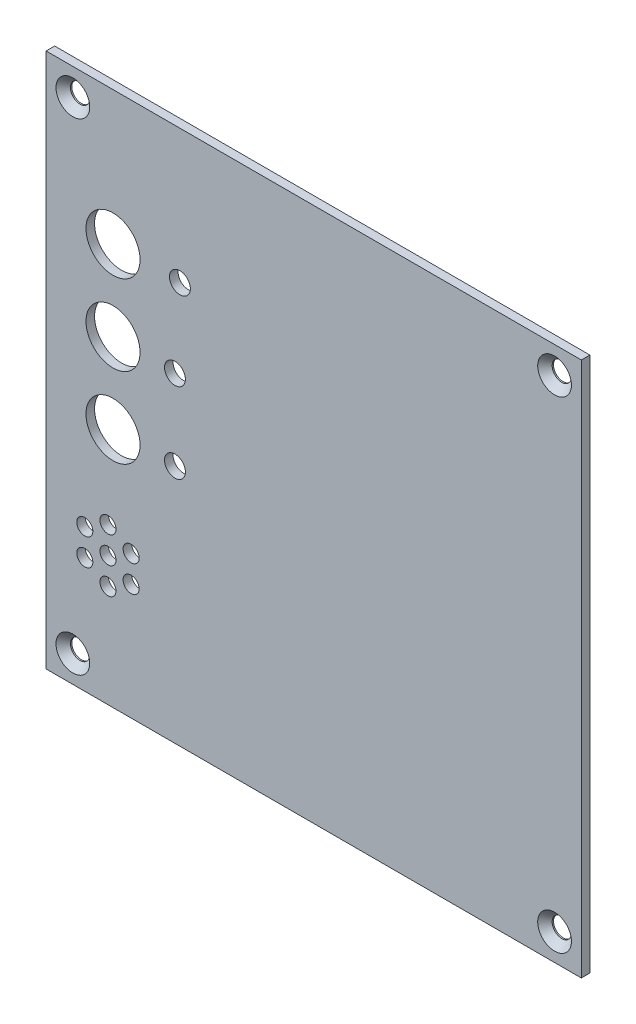
SolidWorks part; units mm, degrees
material "Perspex (TM) Plaque acrylique coulée"
ref_plane "Plan de face" through (0, 0, 0) normal (0, 0, 1) x (1, 0, 0)
ref_plane "Plan de dessus" through (0, 0, 0) normal (0, 1, 0) x (1, 0, 0)
ref_plane "Plan de droite" through (0, 0, 0) normal (1, 0, 0) x (0, 0, -1)
sketch "Esquisse1" plane through (0, 0, 0) normal (0, 0, 1) x (1, 0, 0)
  line L1 (0, 0) -> (100, 0)
  line L2 (0, 0) -> (0, 100)
  line L3 (0, 100) -> (100, 100)
  line L4 (100, 0) -> (100, 100)
  dimension "D1" = 100
  dimension "D2" = 100
extrude "Boss.-Extru.1" add sketch "Esquisse1" along normal blind 1.6
hole_wizard "Fraisage pour vis à tête fraisée M31" positions "Esquisse3D1" profile "Esquisse3" countersink size "M3" standard "ISO" end condition through all
sketch3d "Esquisse3D1"
  line L0 (100, 100, 1.6) -> (0, 100, 1.6) construction
  line L1 (0, 100, 1.6) -> (0, 0, 1.6) construction
  line L2 (100, 0, 1.6) -> (100, 100, 1.6) construction
  line L3 (0, 0, 1.6) -> (100, 0, 1.6) construction
  point P0 (5, 95, 1.6)
  point P2 (95, 95, 1.6)
  point P4 (95, 5, 1.6)
  point P6 (5, 5, 1.6)
  dimension "D1" = 5
  dimension "D2" = 5
  dimension "D3" = 5
  dimension "D4" = 5
  dimension "D5" = 5
  dimension "D6" = 5
  dimension "D7" = 5
  dimension "D8" = 5
sketch "Esquisse3" plane through (5, 95, 1.6) normal (1, 0, 0) x (0, -1, 0)
  line L0 (0, 0) -> (0, 1.6)
  line L1 (0, 1.6) -> (1.8, 1.6)
  line L2 (1.8, 1.6) -> (1.8, 1.35)
  line L3 (1.8, 1.35) -> (3.15, 0)
  line L5 (3.15, 0) -> (0, 0)
  line L6 (-1.8, 1.35) -> (-3.15, 0) construction
  line L11 (0, -6.35) -> (0, 107.95) construction
  dimension "Diamètre du perçage jusqu'au prochain" = 3.6
  dimension "Profondeur du perçage jusqu'au prochain" = 1.6
  dimension "Diamètre du fraisage entrant" = 6.3
  dimension "Angle du fraisage entrant" = 90
sketch "Esquisse4" plane through (0, 0, 1.6) normal (0, 0, 1) x (1, 0, 0)
  line L0 (0, 0) -> (100, 0) construction
  line L2 (0, 100) -> (0, 0) construction
  circle A1 centre (11.557, 24.13) radius 1.5
  circle A3 centre (11.557, 29.13) radius 1.5
  circle A4 centre (15.8871, 26.63) radius 1.5
  circle A5 centre (15.8871, 21.63) radius 1.5
  circle A6 centre (11.557, 19.13) radius 1.5
  circle A7 centre (7.2269, 21.63) radius 1.5
  circle A8 centre (7.2269, 26.63) radius 1.5
  circle A12 centre (12.5, 75) radius 5.05
  circle A13 centre (12.5, 60) radius 5.05
  circle A14 centre (12.5, 45) radius 5.05
  circle A15 centre (25, 75) radius 1.95
  circle A16 centre (24.0718, 59.8692) radius 1.95
  circle A17 centre (24.0718, 44.8692) radius 1.95
  point P25 (11.557, 24.13)
  point P31 (0, 0)
  point P32 (0, 0)
  point P34 (36.5794, 27.5686)
  dimension "D1" = 25
  dimension "D3" = 11.557
  dimension "D5" = 6
  dimension "D7" = 3
  dimension "D2" = 75
  dimension "D4" = 24.13
  dimension "D6" = 11.557
  dimension "D9" = 29.13
extrude "Enlèv. mat.-Extru.1" cut sketch "Esquisse4" against normal through all
sketch "Esquisse5" plane through (0, 0, 1.6) normal (0, 0, 1) x (1, 0, 0)
  line L0 (0, 100) -> (0, 0) construction
  line L1 (100, 0) -> (100, 100) construction
  line L2 (0, 0) -> (100, 0) construction
  text T0 "OCCUPÉ" font "Arial" height 3.5
  text T1 "ATTENDEZ" font "Arial" height 3.5
  text T2 "ENTREZ" font "Arial" height 3.5
  text T3 "SONNETTE" font "Arial" height in points 28
  dimension "D7" = 80
  dimension "D1" = 30
  dimension "D2" = 73
  dimension "D3" = 58
  dimension "D4" = 30
  dimension "D5" = 30
  dimension "D6" = 43
  dimension "D8" = 5
